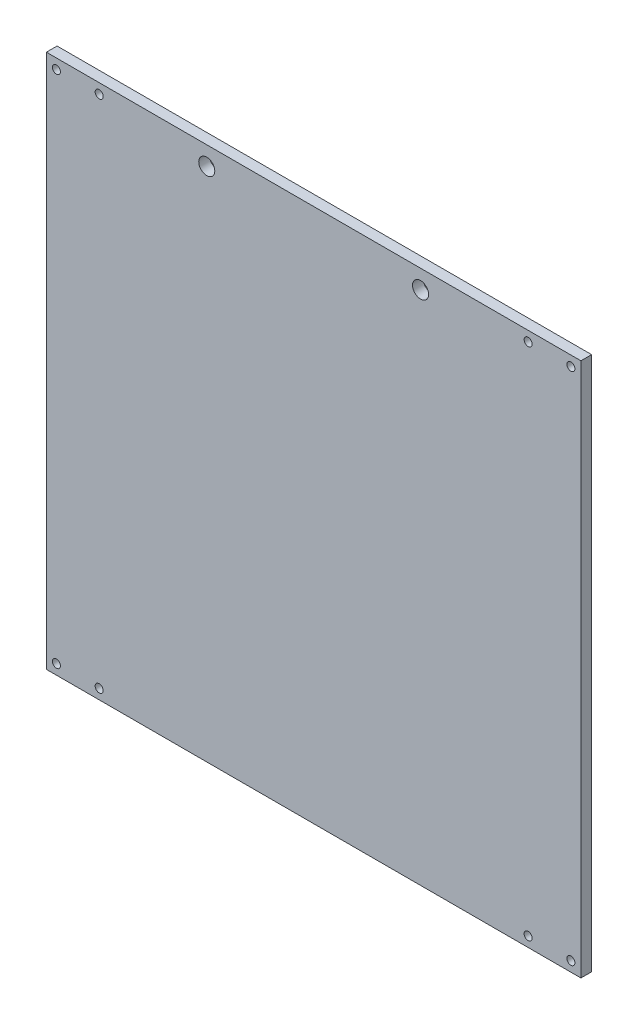
SolidWorks part; units mm, degrees
ref_plane "Front Plane" through (0, 0, 0) normal (0, 0, 1) x (1, 0, 0)
ref_plane "Top Plane" through (0, 0, 0) normal (0, 1, 0) x (1, 0, 0)
ref_plane "Right Plane" through (0, 0, 0) normal (1, 0, 0) x (0, 0, -1)
sketch "Sketch1" plane through (0, 0, 0) normal (0, 0, 1) x (1, 0, 0)
  line L1 (-100, -100) -> (100, -100)
  line L2 (-100, -100) -> (-100, 100)
  line L3 (-100, 100) -> (100, 100)
  line L4 (100, -100) -> (100, 100)
  line L5 (-100, -100) -> (100, 100) construction
  line L6 (-100, 100) -> (100, -100) construction
  point P0 (0, 0)
  dimension "D1" = 200
  dimension "D2" = 200
extrude "Boss-Extrude1" add sketch "Sketch1" along normal blind 4
hole_wizard "Ø3.0mm Dowel Hole1" positions "Sketch4" profile "Sketch5" hole size "Ø3.0" standard "ANSI Metric" end condition up to next
sketch "Sketch4" plane through (0, 0, 4) normal (0, 0, 1) x (1, 0, 0)
  line L0 (-80.25, 96.25) -> (-96.25, 96.25) construction
  line L1 (100, 100) -> (-100, 100) construction
  line L2 (-100, 100) -> (-100, -100) construction
  point P0 (-80.25, 96.25)
  point P3 (-96.25, 96.25)
  dimension "D1" = 16
  dimension "D2" = 3.75
  dimension "D3" = 3.75
sketch "Sketch5" plane through (-80.25, 96.25, 4) normal (1, 0, 0) x (0, -1, 0)
  line L0 (0, 0) -> (0, 4.001)
  line L1 (0, 4.001) -> (1.5, 4.001)
  line L2 (1.5, 4.001) -> (1.5, 0)
  line L5 (1.5, 0) -> (0, 0)
  line L11 (0, -6.35) -> (0, 107.95) construction
  dimension "Thru Hole Dia." = 3
  dimension "Thru Hole Depth" = 4.001
ref_plane "Plane1" through (0, 0, 0) normal (-1, 0, 0) x (0, 0, 1)
mirror "Mirror1" about plane through (0, 0, 0) normal (-1, 0, 0) of "Ø3.0mm Dowel Hole1"
ref_plane "Plane2" through (0, 0, 0) normal (0, 1, 0) x (1, 0, 0)
mirror "Mirror2" about plane through (0, 0, 0) normal (0, 1, 0) of "Mirror1", "Ø3.0mm Dowel Hole1"
sketch "Sketch6" plane through (0, 0, 0) normal (0, 0, -1) x (-1, 0, 0)
  line L0 (-40, 93) -> (40, 93) construction
  line L5 (-100, 100) -> (100, 100) construction
  line L6 (0, 100) -> (0, -100) construction
  line L7 (100, -100) -> (-100, -100) construction
  circle A0 centre (-40, 93) radius 3
  circle A1 centre (40, 93) radius 3
  point P6 (0, 93)
  point P11 (-41.7345, 90)
  dimension "D1" = 6
  dimension "D2" = 7
  dimension "D3" = 80
extrude "Cut-Extrude1" cut sketch "Sketch6" against normal up to next
